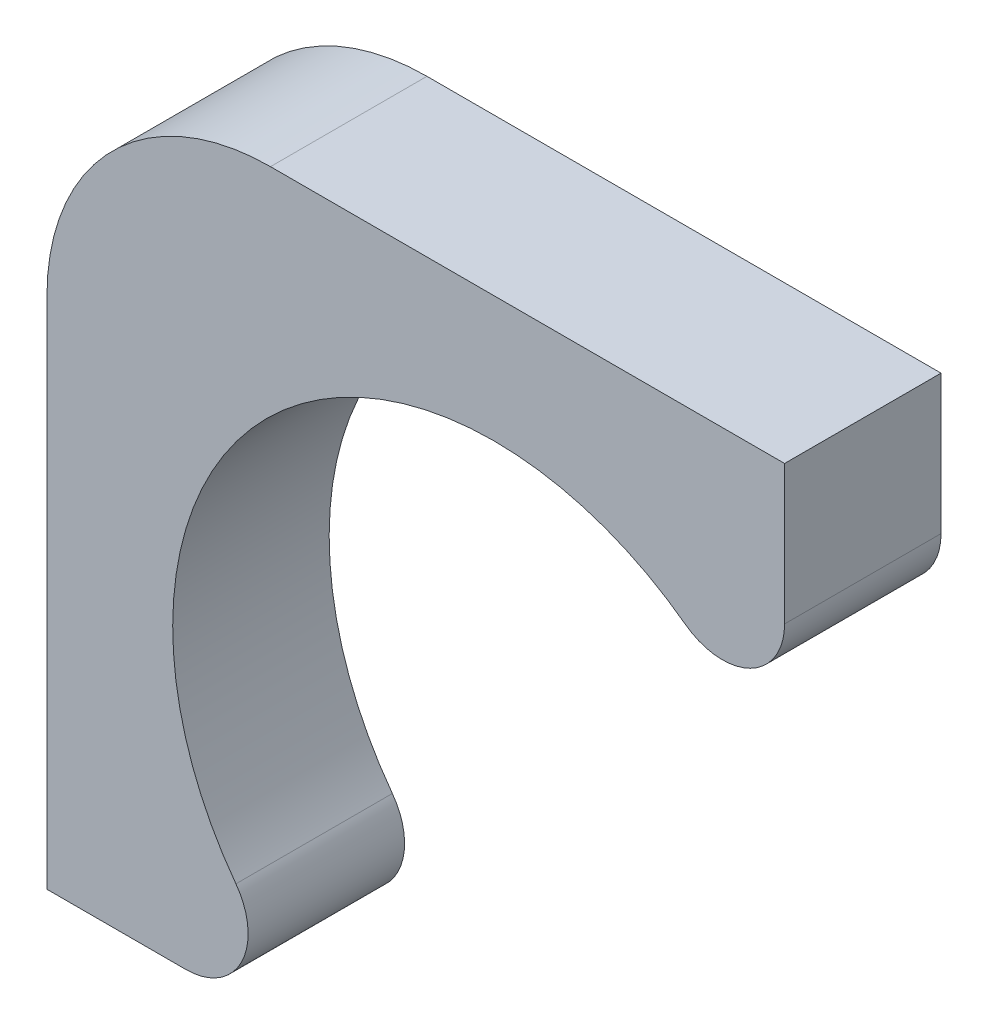
SolidWorks part; units mm, degrees
material "POLIURETANO (11671)"
ref_plane "Alzado" through (0, 0, 0) normal (0, 0, 1) x (1, 0, 0)
ref_plane "Planta" through (0, 0, 0) normal (0, 1, 0) x (1, 0, 0)
ref_plane "Vista lateral" through (0, 0, 0) normal (1, 0, 0) x (0, 0, -1)
sketch "Croquis1" plane through (0, 0, 0) normal (0, 0, 1) x (1, 0, 0)
  line L0 (2.6, 4) -> (-2, 4)
  line L1 (-4, 2) -> (-4, -2.6)
  line L2 (0, 0) -> (0, 4) construction
  line L3 (0, 0) -> (-4, 0) construction
  line L4 (2.6, 4) -> (2.6, 2.7563)
  line L5 (-4, -2.6) -> (-2.7563, -2.6)
  arc A0 (-2.3094, -1.7123) -> (1.7123, 2.3094) centre (0, 0) cw
  arc A1 (-2, 4) -> (-4, 2) centre (-2, 2) ccw
  arc A2 (2.6, 2.7563) -> (1.7123, 2.3094) centre (2.0437, 2.7563) cw
  arc A3 (-2.7563, -2.6) -> (-2.3094, -1.7123) centre (-2.7563, -2.0437) ccw
  point P15 (2.0437, 2.2)
  dimension "D1" = 2.875
  dimension "D3" = 2
  dimension "D2" = 4
  dimension "D4" = 6.6
  dimension "D5" = 1.8
extrude "Saliente-Extruir1" add sketch "Croquis1" along normal blind 1.4
